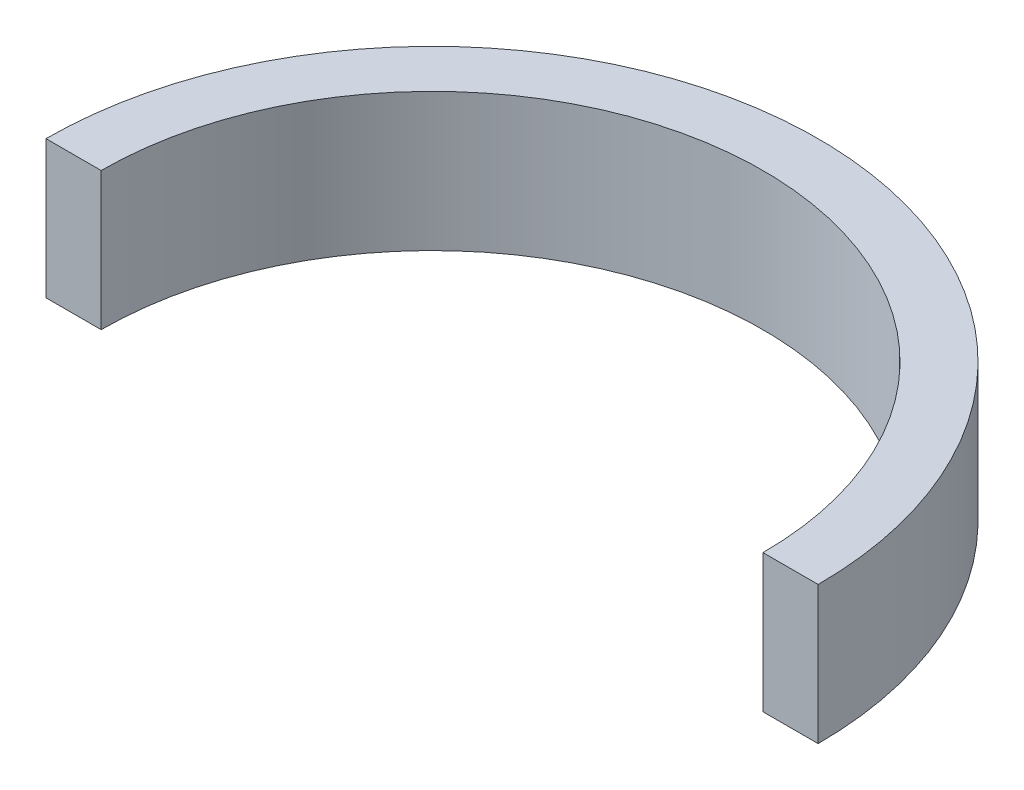
SolidWorks part; units mm, degrees
ref_plane "前视基准面" through (0, 0, 0) normal (0, 0, 1) x (1, 0, 0)
ref_plane "上视基准面" through (0, 0, 0) normal (0, 1, 0) x (1, 0, 0)
ref_plane "右视基准面" through (0, 0, 0) normal (1, 0, 0) x (0, 0, -1)
sketch "草图1" plane through (0, 0, 0) normal (0, 1, 0) x (1, 0, 0)
  line L0 (0, 0) -> (18.1506, 0) construction
  line L1 (-56, 0) -> (-48, 0)
  line L2 (48, 0) -> (56, 0)
  arc A0 (-56, 0) -> (56, 0) centre (0, 0) cw
  arc A1 (-48, 0) -> (48, 0) centre (0, 0) cw
extrude "凸台-拉伸1" add sketch "草图1" along normal blind 20
